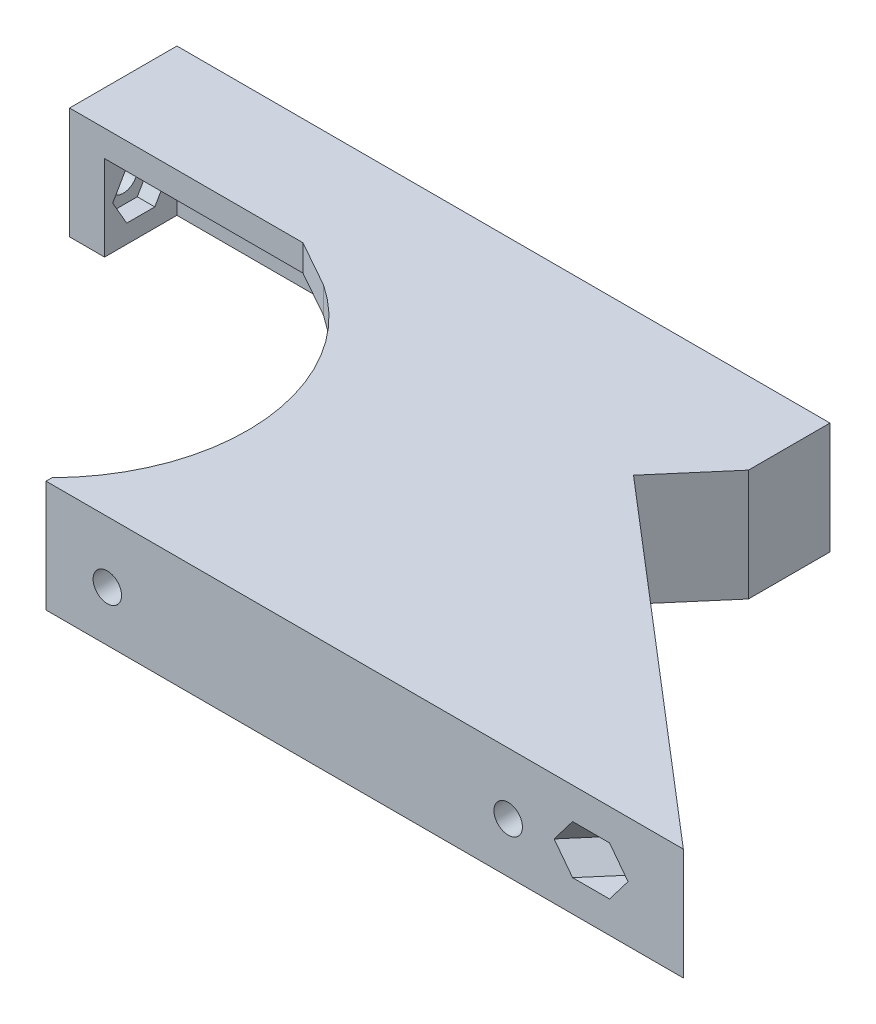
SolidWorks part; units mm, degrees
ref_plane "Alzado" through (0, 0, 0) normal (0, 0, 1) x (1, 0, 0)
ref_plane "Planta" through (0, 0, 0) normal (0, 1, 0) x (1, 0, 0)
ref_plane "Vista lateral" through (0, 0, 0) normal (1, 0, 0) x (0, 0, -1)
sketch "Croquis1" plane through (0, 0, 0) normal (0, 1, 0) x (1, 0, 0)
  line L0 (0, 0) -> (72.7832, 0)
  line L1 (72.7832, 0) -> (38.2245, 29.6204)
  line L2 (38.2245, 29.6204) -> (35.6214, 26.5833)
  line L3 (35.6214, 26.5833) -> (60.8031, 5)
  line L4 (60.8031, 5) -> (0, 5)
  line L5 (0, 5) -> (0, 0)
  dimension "D1" = 4
  dimension "D2" = 5
  dimension "D3" = 40.6
  dimension "D4" = 72.7832
extrude "Saliente-Extruir1" add sketch "Croquis1" along normal blind 12.75
sketch "Croquis2" plane through (0, 0, 0) normal (0, 0, 1) x (1, 0, 0)
  line L2 (0, 12.75) -> (72.7832, 12.75) construction
  line L3 (72.7832, 12.75) -> (72.7832, 0) construction
  circle A0 centre (52.7832, 5.75) radius 1.625
  circle A1 centre (7, 5.75) radius 1.625
  dimension "D1" = 3.25
  dimension "D2" = 20
  dimension "D3" = 7
  dimension "D4" = 45.7832
  dimension "D5" = 7
extrude "Cortar-Extruir1" cut sketch "Croquis2" against normal up to next
sketch "Croquis3" plane through (0, 12.75, 0) normal (0, 1, 0) x (1, 0, 0)
  line L0 (0, 5) -> (0, 0) construction
  line L1 (0, 0) -> (72.7832, 0) construction
  circle A0 centre (-16, 16.5) radius 22.5
  dimension "D1" = 45
  dimension "D2" = 16
  dimension "D3" = 16.5
extrude "Cortar-Extruir2" cut sketch "Croquis3" against normal through all
sketch "Croquis4" plane through (0, 12.75, 0) normal (0, 1, 0) x (1, 0, 0)
  line L0 (38.2245, 29.6204) -> (31.6563, 35.25)
  line L1 (31.6563, 35.25) -> (-3.5627, 35.25)
  line L2 (0, 0) -> (72.7832, 0) construction
  line L3 (72.7832, 0) -> (38.2245, 29.6204) construction
  line L4 (38.2245, 29.6204) -> (35.6214, 26.5833)
  line L5 (35.6214, 26.5833) -> (60.8031, 5)
  line L6 (60.8031, 5) -> (3.3391, 5)
  arc A0 (3.3391, 5) -> (-3.5627, 35.25) centre (-16, 16.5) ccw
  arc A1 (0, 0.6807) -> (3.3391, 5) centre (-16, 16.5) ccw construction
  dimension "D1" = 35.25
extrude "Saliente-Extruir2" add sketch "Croquis4" against normal blind 3
sketch "Croquis5" plane through (0, 9.75, 0) normal (0, -1, 0) x (1, 0, 0)
  line L0 (-3.5627, -35.25) -> (31.6563, -35.25)
  line L1 (31.6563, -35.25) -> (38.2245, -29.6204)
  line L2 (38.2245, -29.6204) -> (35.6214, -26.5833)
  line L3 (35.6214, -26.5833) -> (30.1767, -31.25)
  line L4 (30.1767, -31.25) -> (0.9908, -31.25)
  arc A0 (-3.5627, -35.25) -> (3.3391, -5) centre (-16, -16.5) ccw construction
  arc A1 (-3.5627, -35.25) -> (0.9908, -31.25) centre (-16, -16.5) ccw
  dimension "D1" = 4
extrude "Saliente-Extruir3" add sketch "Croquis5" along normal up to vertex (9.75 mm away)
sketch "Croquis6" plane through (30.8242, 0, -35.9632) normal (0.6508, 0, -0.7593) x (-0.7593, 0, -0.6508)
  line L0 (-55.2622, 12.75) -> (-55.2622, 0) construction
  circle A0 centre (-47.2622, 6.375) radius 1.625
  circle A1 centre (-7.4422, 6.375) radius 1.625
  dimension "D1" = 3.25
  dimension "D2" = 3.25
  dimension "D3" = 8
  dimension "D5" = 39.82
extrude "Cortar-Extruir3" cut sketch "Croquis6" against normal blind 10
sketch "Croquis7" plane through (28.2211, 0, -32.9261) normal (-0.6508, 0, 0.7593) x (0.7593, 0, 0.6508)
  line L1 (48.8643, 3.6) -> (50.4665, 6.375)
  line L2 (50.4665, 6.375) -> (48.8643, 9.15)
  line L3 (48.8643, 9.15) -> (45.66, 9.15)
  line L4 (45.66, 9.15) -> (44.0579, 6.375)
  line L5 (44.0579, 6.375) -> (45.66, 3.6)
  line L6 (45.66, 3.6) -> (48.8643, 3.6)
  circle A0 centre (47.2622, 6.375) radius 2.775 construction
  dimension "D1" = 5.55
extrude "Cortar-Extruir4" cut sketch "Croquis7" along normal blind 10 from offset 2 offset against normal yes
sketch "Croquis8" plane through (28.2211, 0, -32.9261) normal (-0.6508, 0, 0.7593) x (0.7593, 0, 0.6508)
  line L0 (45.66, 3.6) -> (48.8643, 3.6) construction
  line L1 (9.0443, 3.6) -> (10.6465, 6.375)
  line L2 (10.6465, 6.375) -> (9.0443, 9.15)
  line L3 (9.0443, 9.15) -> (5.84, 9.15)
  line L4 (5.84, 9.15) -> (4.2379, 6.375)
  line L5 (4.2379, 6.375) -> (5.84, 3.6)
  line L6 (5.84, 3.6) -> (9.0443, 3.6)
  circle A0 centre (7.4422, 6.375) radius 2.775 construction
extrude "Cortar-Extruir5" cut sketch "Croquis8" along normal blind 10 from offset 2 offset against normal yes
sketch "Croquis9" plane through (0, 0, -5) normal (0, 0, -1) x (-1, 0, 0)
  line L1 (-5.3979, 2.975) -> (-3.7957, 5.75)
  line L2 (-3.7957, 5.75) -> (-5.3979, 8.525)
  line L3 (-5.3979, 8.525) -> (-8.6021, 8.525)
  line L4 (-8.6021, 8.525) -> (-10.2043, 5.75)
  line L5 (-10.2043, 5.75) -> (-8.6021, 2.975)
  line L6 (-8.6021, 2.975) -> (-5.3979, 2.975)
  line L7 (-51.1811, 2.975) -> (-49.5789, 5.75)
  line L8 (-49.5789, 5.75) -> (-51.1811, 8.525)
  line L9 (-51.1811, 8.525) -> (-54.3853, 8.525)
  line L10 (-54.3853, 8.525) -> (-55.9875, 5.75)
  line L11 (-55.9875, 5.75) -> (-54.3853, 2.975)
  line L12 (-54.3853, 2.975) -> (-51.1811, 2.975)
  circle A0 centre (-7, 5.75) radius 2.775 construction
  circle A1 centre (-52.7832, 5.75) radius 2.775 construction
  dimension "D1" = 5.55
extrude "Cortar-Extruir6" cut sketch "Croquis9" against normal blind 2
sketch "Croquis10" plane through (0, 0, -35.25) normal (0, 0, -1) x (-1, 0, 0)
  line L0 (-31.6563, 0) -> (-31.6563, 12.75) construction
  circle A0 centre (-21.6563, 6.375) radius 1.625
  dimension "D1" = 3.25
  dimension "D2" = 10
extrude "Cortar-Extruir7" cut sketch "Croquis10" against normal up to next
sketch "Croquis11" plane through (0, 0, -31.25) normal (0, 0, 1) x (1, 0, 0)
  line L1 (23.2585, 3.6) -> (24.8606, 6.375)
  line L2 (24.8606, 6.375) -> (23.2585, 9.15)
  line L3 (23.2585, 9.15) -> (20.0542, 9.15)
  line L4 (20.0542, 9.15) -> (18.452, 6.375)
  line L5 (18.452, 6.375) -> (20.0542, 3.6)
  line L6 (20.0542, 3.6) -> (23.2585, 3.6)
  circle A0 centre (21.6563, 6.375) radius 2.775 construction
  dimension "D1" = 5.55
extrude "Cortar-Extruir8" cut sketch "Croquis11" against normal blind 2
mirror "Simetría1" about plane through (0, 0, 0) normal (0, 1, 0) of bodies 111
sketch "Croquis12" plane through (0, 0, -35.25) normal (0, 0, -1) x (-1, 0, 0)
  line L1 (-79.3319, 0) -> (13.1768, 0)
  line L2 (-79.3319, 0) -> (-79.3319, 24.2558)
  line L3 (-79.3319, 24.2558) -> (13.1768, 24.2558)
  line L4 (13.1768, 0) -> (13.1768, 24.2558)
extrude "Cortar-Extruir9" cut sketch "Croquis12" against normal through all both and the other way through all
sketch "Croquis13" plane through (0, -12.75, 0) normal (0, -1, 0) x (1, 0, 0)
  line L1 (-35.5627, -82.3826) -> (-35.5627, -38.25)
  line L3 (-3.5627, -35.25) -> (31.6563, -35.25)
  line L5 (31.6563, -35.25) -> (0.0002, -62.3826)
  line L6 (0.0002, -62.3826) -> (-35.5627, -82.3826)
  line L7 (72.7832, 0) -> (31.6563, -35.25) construction
  line L8 (-3.5627, -35.25) -> (-8.9133, -38.25)
  line L9 (-8.9133, -38.25) -> (-35.5627, -38.25)
  dimension "D1" = 32
  dimension "D2" = 3
  dimension "D3" = 20
extrude "Saliente-Extruir4" add sketch "Croquis13" against normal up to vertex (12.75 mm away)
sketch "Croquis14" plane through (0, 0, 0) normal (0, 1, 0) x (1, 0, 0)
  line L3 (30.1767, 31.25) -> (0.9908, 31.25)
  line L4 (0.9908, 31.25) -> (-31.5627, 38.25)
  line L6 (-31.5627, 38.25) -> (-31.5627, 75.5439)
  line L7 (-2.3039, 59.0892) -> (70.1801, -3.0371)
  line L8 (-31.5627, 75.5439) -> (-2.3039, 59.0892)
  line L9 (-31.5627, 38.25) -> (-31.5627, 75.5439)
  line L10 (-2.3039, 59.0892) -> (30.1767, 31.25)
  line L11 (-31.5627, 75.5439) -> (-2.3039, 59.0892)
  dimension "D1" = 4
extrude "Cortar-Extruir10" cut sketch "Croquis14" against normal up to vertex
sketch "Croquis16" plane through (30.8242, 0, -35.9632) normal (0.6508, 0, -0.7593) x (-0.7593, 0, -0.6508)
  line L0 (40.5969, 0) -> (-55.2622, 0) construction
  line L1 (-27.4422, 0) -> (40.5969, 0)
  line L2 (-27.4422, 0) -> (-27.4422, -12.75)
  line L3 (-27.4422, -12.75) -> (40.5969, -12.75)
  line L4 (40.5969, 0) -> (40.5969, -12.75)
  circle A0 centre (-7.4422, -6.375) radius 1.625 construction
  dimension "D1" = 20
  dimension "D2" = 68.0391
extrude "Cortar-Extruir11" cut sketch "Croquis16" against normal blind 1
sketch "Croquis17" plane through (0, -12.75, 0) normal (0, -1, 0) x (1, 0, 0)
  line L1 (0.0002, -61.6233) -> (-40.6573, -61.6233)
  line L2 (0.0002, -61.6233) -> (0.0002, -84.5579)
  line L3 (0.0002, -84.5579) -> (-40.6573, -84.5579)
  line L4 (-40.6573, -61.6233) -> (-40.6573, -84.5579)
extrude "Cortar-Extruir12" cut sketch "Croquis17" against normal through all both and the other way through all
sketch "Croquis18" plane through (0, 0, 0) normal (0, 1, 0) x (1, 0, 0)
  line L0 (60.8031, 5) -> (-2.3039, 59.0892) construction
  line L1 (-35.5627, 61.6233) -> (-0.6506, 61.6233)
  line L2 (-35.5627, 61.6233) -> (-35.5627, 57.6722)
  line L3 (-35.5627, 57.6722) -> (-0.6506, 57.6722)
  line L4 (-0.6506, 61.6233) -> (-0.6506, 57.6722)
extrude "Saliente-Extruir5" add sketch "Croquis18" against normal up to surface (9.75 mm away)
sketch "Croquis20" plane through (30.1734, 0, -35.2039) normal (0.6508, 0, -0.7593) x (-0.7593, 0, -0.6508)
  line L2 (40.5969, -12.75) -> (40.5969, 0) construction
  circle A0 centre (25.5969, -6.375) radius 1.625
  circle A1 centre (-7.4422, -6.375) radius 1.625 construction
  circle A2 centre (-7.4422, -6.375) radius 1.625
  dimension "D2" = 33.0391
  dimension "D1" = 15
extrude "Cortar-Extruir14" cut sketch "Croquis20" against normal blind 10
sketch "Croquis21" plane through (28.2211, 0, -32.9261) normal (-0.6508, 0, 0.7593) x (0.7593, 0, 0.6508)
  line L0 (9.0443, -9.15) -> (5.84, -9.15) construction
  line L1 (-23.9947, -9.15) -> (-22.3926, -6.375)
  line L2 (-22.3926, -6.375) -> (-23.9947, -3.6)
  line L3 (-23.9947, -3.6) -> (-27.199, -3.6)
  line L4 (-27.199, -3.6) -> (-28.8012, -6.375)
  line L5 (-28.8012, -6.375) -> (-27.199, -9.15)
  line L6 (-27.199, -9.15) -> (-23.9947, -9.15)
  circle A0 centre (-25.5969, -6.375) radius 2.775 construction
extrude "Cortar-Extruir15" cut sketch "Croquis21" against normal up to vertex (2 mm away) up to point (36.3898, -9.15, -28.5588)
sketch "Croquis22" plane through (0, 0, -61.6233) normal (0, 0, -1) x (-1, 0, 0)
  line L0 (35.5627, -12.75) -> (35.5627, 0) construction
  circle A0 centre (18.1127, -6.375) radius 1.625
  dimension "D1" = 3.25
  dimension "D2" = 17.45
extrude "Cortar-Extruir16" cut sketch "Croquis22" against normal blind 10
sketch "Croquis23" plane through (0, 0, -57.6722) normal (0, 0, 1) x (1, 0, 0)
  line L0 (7.5697, -9.15) -> (10.0026, -9.15) construction
  line L1 (-16.5105, -9.15) -> (-14.9084, -6.375)
  line L2 (-14.9084, -6.375) -> (-16.5105, -3.6)
  line L3 (-16.5105, -3.6) -> (-19.7148, -3.6)
  line L4 (-19.7148, -3.6) -> (-21.317, -6.375)
  line L5 (-21.317, -6.375) -> (-19.7148, -9.15)
  line L6 (-19.7148, -9.15) -> (-16.5105, -9.15)
  circle A0 centre (-18.1127, -6.375) radius 2.775 construction
extrude "Cortar-Extruir17" cut sketch "Croquis23" against normal blind 2
sketch "Croquis26" plane through (0, 0, 0) normal (0, 1, 0) x (1, 0, 0)
  line L0 (60.8031, 5) -> (-2.2878, 59.0754)
  line L1 (60.8031, 5) -> (60.1523, 4.2407)
  line L2 (-2.2878, 59.0754) -> (-2.9386, 58.3161)
  line L3 (60.1523, 4.2407) -> (-2.9386, 58.3161)
  line L5 (60.8031, 5) -> (-0.6506, 57.6722) construction
  dimension "D1" = 1
extrude "Saliente-Extruir6" add sketch "Croquis26" against normal up to vertex (12.75 mm away)
sketch "Croquis27" plane through (27.5703, 0, -32.1669) normal (-0.6508, 0, 0.7593) x (0.7593, 0, 0.6508)
  line L0 (9.0443, -9.15) -> (5.84, -9.15) construction
  line L1 (-22.4214, -6.375) -> (-24.0092, -3.625)
  line L2 (-24.0092, -3.625) -> (-27.1846, -3.625)
  line L3 (-27.1846, -3.625) -> (-28.7723, -6.375)
  line L4 (-28.7723, -6.375) -> (-27.1846, -9.125)
  line L5 (-27.1846, -9.125) -> (-24.0092, -9.125)
  line L6 (-24.0092, -9.125) -> (-22.4214, -6.375)
  line L7 (10.6465, -6.375) -> (9.0443, -3.6)
  line L8 (9.0443, -3.6) -> (5.84, -3.6)
  line L9 (5.84, -3.6) -> (4.2379, -6.375)
  line L10 (4.2379, -6.375) -> (5.84, -9.15)
  line L11 (5.84, -9.15) -> (9.0443, -9.15)
  line L12 (9.0443, -9.15) -> (10.6465, -6.375)
  circle A0 centre (-25.5969, -6.375) radius 2.75 construction
  circle A1 centre (7.4422, -6.375) radius 2.775 construction
extrude "Cortar-Extruir18" cut sketch "Croquis27" against normal blind 2
sketch "Croquis28" plane through (29.5227, 0, -34.4447) normal (-0.6508, 0, 0.7593) x (0.7593, 0, 0.6508)
  line L1 (-24.0092, -3.625) -> (-27.1846, -3.625)
  line L2 (-27.1846, -3.625) -> (-28.7723, -6.375)
  line L3 (-28.7723, -6.375) -> (-27.1846, -9.125)
  line L4 (-27.1846, -9.125) -> (-24.0092, -9.125)
  line L5 (-24.0092, -9.125) -> (-22.4214, -6.375)
  line L6 (-22.4214, -6.375) -> (-24.0092, -3.625)
  line L7 (10.6465, -6.375) -> (9.0443, -3.6)
  line L8 (9.0443, -3.6) -> (5.84, -3.6)
  line L9 (5.84, -3.6) -> (4.2379, -6.375)
  line L10 (4.2379, -6.375) -> (5.84, -9.15)
  line L11 (5.84, -9.15) -> (9.0443, -9.15)
  line L12 (9.0443, -9.15) -> (10.6465, -6.375)
  circle A0 centre (-25.5969, -6.375) radius 2.75 construction
  circle A1 centre (7.4422, -6.375) radius 2.775 construction
  circle A2 centre (-25.5969, -6.375) radius 1.625
  circle A3 centre (7.4422, -6.375) radius 1.625
extrude "Saliente-Extruir7" add sketch "Croquis28" along normal blind 1
sketch "Croquis29" plane through (-35.5627, 0, 0) normal (-1, 0, 0) x (0, 0, 1)
  line L0 (-61.6233, -12.75) -> (-61.6233, 0) construction
  line L1 (-38.25, 0) -> (-61.6233, 0) construction
  circle A0 centre (-51.6233, -6.375) radius 1.625
  dimension "D3" = 3.25
  dimension "D1" = 10
  dimension "D2" = 6.375
extrude "Cortar-Extruir19" cut sketch "Croquis29" against normal up to next
sketch "Croquis30" plane through (-31.5627, 0, 0) normal (1, 0, 0) x (0, 0, -1)
  line L8 (53.2255, -9.15) -> (54.8276, -6.375)
  line L9 (54.8276, -6.375) -> (53.2255, -3.6)
  line L10 (53.2255, -3.6) -> (50.0212, -3.6)
  line L11 (50.0212, -3.6) -> (48.419, -6.375)
  line L12 (48.419, -6.375) -> (50.0212, -9.15)
  line L13 (50.0212, -9.15) -> (53.2255, -9.15)
  circle A0 centre (51.6233, -6.375) radius 2.775 construction
  dimension "D1" = 5.55
extrude "Cortar-Extruir20" cut sketch "Croquis30" against normal blind 2
sketch "Croquis40" plane through (0, -12.75, 0) normal (0, -1, 0) x (1, 0, 0)
  line L0 (51.0095, -17.3453) -> (-0.6506, -61.6233)
  line L1 (51.0095, -17.3453) -> (51.6603, -18.1045)
  line L2 (51.6603, -18.1045) -> (0.886, -61.6233)
  line L3 (0.886, -61.6233) -> (-0.6506, -61.6233)
extrude "Saliente-Extruir11" add sketch "Croquis40" against normal up to surface (12.75 mm away) up to face at (7.777, 0, -27.7785)
sketch "Croquis41" plane through (30.8242, 0, -35.9632) normal (0.6508, 0, -0.7593) x (-0.7593, 0, -0.6508)
  circle A0 centre (-7.4422, -6.375) radius 1.625
  circle A1 centre (25.5969, -6.375) radius 1.625
extrude "Cortar-Extruir25" cut sketch "Croquis41" against normal blind 10
sketch "Croquis42" plane through (0, -12.75, 0) normal (0, -1, 0) x (1, 0, 0)
  line L1 (72.7832, 0) -> (0.886, -61.6233) construction
  line L2 (32.9594, -34.1331) -> (39.0181, -41.2019)
  line L3 (39.0181, -41.2019) -> (24.7121, -41.2019)
  line L4 (32.9594, -34.1331) -> (24.7121, -41.2019)
  dimension "D2" = 9.31
extrude "Saliente-Extruir12" add sketch "Croquis42" against normal up to surface (12.75 mm away) up to face at (-0.0029, 0, -29.6064)
sketch "Croquis43" plane through (0, -12.75, 0) normal (0, -1, 0) x (1, 0, 0)
  line L0 (39.0181, -41.2019) -> (39.0181, -50.5119)
  line L1 (39.0181, -50.5119) -> (13.8499, -50.5119)
  line L2 (-35.5627, -38.25) -> (-35.5627, -61.6233) construction
  line L3 (39.0181, -41.2019) -> (24.7121, -41.2019)
  line L4 (24.7121, -41.2019) -> (13.8499, -50.5119)
  dimension "D1" = 9.31
extrude "Saliente-Extruir13" add sketch "Croquis43" against normal up to surface (12.75 mm away) up to face at (6.9041, 0, -31.5862)
sketch "Croquis44" plane through (0, -12.75, 0) normal (0, -1, 0) x (1, 0, 0)
  line L0 (13.8499, -50.5119) -> (-35.5627, -50.5119)
  line L1 (-35.5627, -38.25) -> (-35.5627, -61.6233) construction
  line L2 (-35.5627, -50.5119) -> (-35.5627, -61.6233)
  line L3 (-35.5627, -61.6233) -> (0.886, -61.6233)
  line L4 (0.886, -61.6233) -> (13.8499, -50.5119)
extrude "Cortar-Extruir26" cut sketch "Croquis44" against normal through all
sketch "Croquis45" plane through (0, 0, 0) normal (0, 1, 0) x (1, 0, 0)
  line L0 (6.1668, 50.5119) -> (21.7241, 50.5119)
  line L1 (39.0181, 50.5119) -> (6.1668, 50.5119) construction
  line L2 (21.7241, 50.5119) -> (21.7241, 37.1777)
  line L3 (6.1668, 50.5119) -> (59.2664, 5) construction
  line L4 (21.7241, 37.1777) -> (6.1668, 50.5119)
extrude "Saliente-Extruir14" add sketch "Croquis45" against normal up to surface (9.75 mm away)
sketch "Croquis46" plane through (0, 0, 0) normal (0, 1, 0) x (1, 0, 0)
  line L0 (6.1668, 50.5119) -> (59.2664, 5) construction
  line L1 (-35.5627, 50.5119) -> (-31.5627, 50.5119)
  line L2 (-35.5627, 50.5119) -> (-35.5627, 38.25)
  line L3 (-35.5627, 38.25) -> (-31.5627, 38.25)
  line L4 (-31.5627, 46.5119) -> (-31.5627, 38.25)
  line L5 (-31.5627, 50.5119) -> (10.8337, 50.5119)
  line L7 (-31.5627, 46.5119) -> (10.8337, 46.5119)
  line L8 (10.8337, 50.5119) -> (10.8337, 46.5119)
  dimension "D1" = 4
extrude "Saliente-Extruir15" add sketch "Croquis46" against normal up to surface (9.75 mm away)
sketch "Croquis47" plane through (-35.5627, 0, 0) normal (-1, 0, 0) x (0, 0, 1)
  circle A0 centre (-42.381, -4.875) radius 1.625
  dimension "D1" = 3.25
extrude "Cortar-Extruir27" cut sketch "Croquis47" against normal up to next
sketch "Croquis48" plane through (-35.5627, 0, 0) normal (-1, 0, 0) x (0, 0, 1)
  line L1 (-40.7788, -7.65) -> (-39.1767, -4.875)
  line L2 (-39.1767, -4.875) -> (-40.7788, -2.1)
  line L3 (-40.7788, -2.1) -> (-43.9831, -2.1)
  line L4 (-43.9831, -2.1) -> (-45.5853, -4.875)
  line L5 (-45.5853, -4.875) -> (-43.9831, -7.65)
  line L6 (-43.9831, -7.65) -> (-40.7788, -7.65)
  circle A0 centre (-42.381, -4.875) radius 2.775 construction
  dimension "D1" = 5.55
extrude "Cortar-Extruir28" cut sketch "Croquis48" against normal up to next from offset 2 offset against normal yes
sketch "Croquis49" plane through (0, 0, 0) normal (0, 1, 0) x (1, 0, 0)
  line L0 (26.6685, 32.9398) -> (35.0181, 42.6816)
  line L1 (10.8337, 46.5119) -> (59.2664, 5) construction
  line L2 (35.0181, 42.6816) -> (35.0181, 46.5119)
  line L3 (35.0181, 46.5119) -> (10.8337, 46.5119)
  line L4 (10.8337, 46.5119) -> (26.6685, 32.9398)
  line L5 (39.0181, 41.2019) -> (39.0181, 50.5119) construction
  line L6 (32.9594, 34.1331) -> (39.0181, 41.2019) construction
  dimension "D1" = 4
  dimension "D2" = 4
extrude "Cortar-Extruir29" cut sketch "Croquis49" against normal up to surface (9.75 mm away)
sketch "Croquis50" plane through (0, 0, -50.5119) normal (0, 0, -1) x (-1, 0, 0)
  line L0 (35.5627, 0) -> (35.5627, -12.75) construction
  line L1 (31.5627, -9.75) -> (-35.0181, -9.75) construction
  circle A0 centre (25.5627, -6.75) radius 1.625
  circle A1 centre (-24.4373, -6.75) radius 1.625
  dimension "D1" = 3.25
  dimension "D2" = 3.25
  dimension "D4" = 50
  dimension "D5" = 3
  dimension "D3" = 10
extrude "Cortar-Extruir30" cut sketch "Croquis50" against normal up to next
sketch "Croquis51" plane through (0, 0, -50.5119) normal (0, 0, -1) x (-1, 0, 0)
  line L1 (-22.8352, -9.525) -> (-21.233, -6.75)
  line L2 (-21.233, -6.75) -> (-22.8352, -3.975)
  line L3 (-22.8352, -3.975) -> (-26.0395, -3.975)
  line L4 (-26.0395, -3.975) -> (-27.6416, -6.75)
  line L5 (-27.6416, -6.75) -> (-26.0395, -9.525)
  line L6 (-26.0395, -9.525) -> (-22.8352, -9.525)
  line L7 (27.1648, -9.525) -> (28.767, -6.75)
  line L8 (28.767, -6.75) -> (27.1648, -3.975)
  line L9 (27.1648, -3.975) -> (23.9605, -3.975)
  line L10 (23.9605, -3.975) -> (22.3584, -6.75)
  line L11 (22.3584, -6.75) -> (23.9605, -9.525)
  line L12 (23.9605, -9.525) -> (27.1648, -9.525)
  circle A0 centre (-24.4373, -6.75) radius 2.775 construction
  circle A1 centre (25.5627, -6.75) radius 2.775 construction
  dimension "D1" = 5.55
extrude "Cortar-Extruir31" cut sketch "Croquis51" against normal up to next from offset 2 offset against normal yes
mirror "Simetría2" of bodies 148 118
sketch "Croquis19" plane through (0, 0, -61.6233) normal (0, 0, -1) x (-1, 0, 0)
  line L1 (-78.7832, -12.75) -> (41.6655, -12.75)
  line L2 (-78.7832, -12.75) -> (-78.7832, 20.1367)
  line L3 (-78.7832, 20.1367) -> (41.6655, 20.1367)
  line L4 (41.6655, -12.75) -> (41.6655, 20.1367)
extrude "Cortar-Extruir13" cut sketch "Croquis19" against normal through all both and the other way through all
